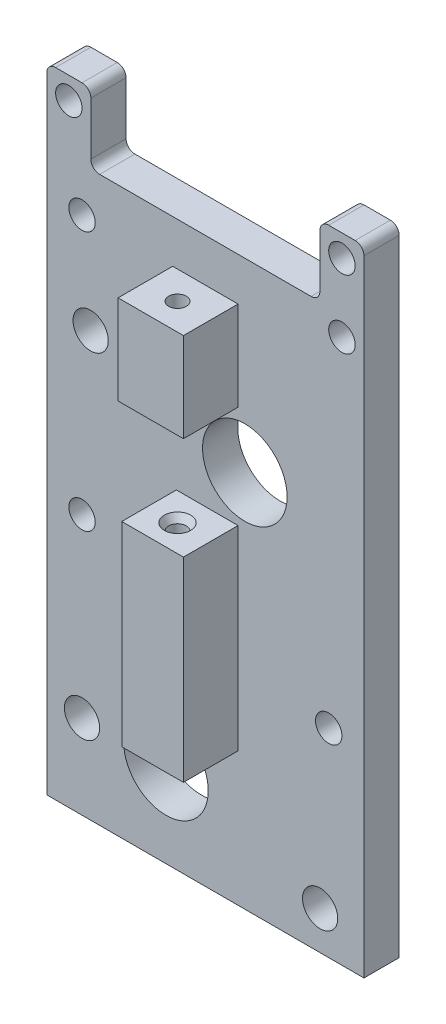
SolidWorks part; units mm, degrees
ref_plane "Front Plane" through (0, 0, 0) normal (0, 0, 1) x (1, 0, 0)
ref_plane "Top Plane" through (0, 0, 0) normal (0, 1, 0) x (1, 0, 0)
ref_plane "Right Plane" through (0, 0, 0) normal (1, 0, 0) x (0, 0, -1)
sketch "Sketch1" plane through (0, 0, 0) normal (0, 0, 1) x (1, 0, 0)
  line L0 (18, 32) -> (18, 39)
  line L1 (-18, -32) -> (18, -32)
  line L2 (-18, -32) -> (-18, 32)
  line L4 (18, -32) -> (18, 32)
  line L5 (-18, -32) -> (18, 32) construction
  line L6 (-18, 32) -> (18, -32) construction
  line L7 (-18, 32) -> (-18, 39)
  line L8 (-17, 40) -> (-14, 40)
  line L10 (-13, 39) -> (-13, 33)
  line L11 (-12, 32) -> (12, 32)
  line L12 (13, 33) -> (13, 39)
  line L13 (14, 40) -> (17, 40)
  arc A0 (18, 39) -> (17, 40) centre (17, 39) ccw
  arc A1 (13, 39) -> (14, 40) centre (14, 39) cw
  arc A2 (-13, 39) -> (-14, 40) centre (-14, 39) ccw
  arc A3 (-18, 39) -> (-17, 40) centre (-17, 39) cw
  arc A4 (12, 32) -> (13, 33) centre (12, 33) ccw
  arc A5 (-13, 33) -> (-12, 32) centre (-12, 33) ccw
  point P0 (0, 0)
  point P14 (13, 40)
  dimension "D1" = 1
  dimension "D2" = 1
extrude "Boss-Extrude1" add sketch "Sketch1" along normal blind 4
sketch "Sketch2" plane through (0, 0, 4) normal (0, 0, 1) x (1, 0, 0)
  line L2 (-4.475, -22.4429) -> (13.025, -22.4429) construction
  line L3 (4.475, 10.9277) -> (-13.025, 10.9277) construction
  line L4 (-13.025, 10.9277) -> (-13.025, 16.1277) construction
  line L5 (13.025, -22.4429) -> (13.025, -27.6429) construction
  circle A0 centre (15.5, 29.7441) radius 1.5
  circle A1 centre (-14, 27) radius 1.5
  circle A2 centre (4.475, 10.9277) radius 4.8
  circle A3 centre (-14, -2.4429) radius 1.5
  circle A4 centre (14, -9.4429) radius 1.5
  circle A5 centre (-4.475, -22.4429) radius 4.8
  circle A6 centre (13.025, -27.6429) radius 2
  circle A7 centre (-14, -22.4429) radius 2
  circle A8 centre (-13.025, 16.1277) radius 2
  circle A9 centre (15.5, 37.5) radius 1.5
  circle A10 centre (-15.5, 37.5) radius 1.5
extrude "Cut-Extrude1" cut sketch "Sketch2" against normal blind 10
sketch "Sketch3" plane through (0, 0, 4) normal (0, 0, 1) x (1, 0, 0)
  line L1 (-3.2906, -16.814) -> (3.7094, -16.814)
  line L2 (-3.2906, -16.814) -> (-3.2906, 5.3322)
  line L3 (-3.2906, 5.3322) -> (3.7094, 5.3322)
  line L4 (3.7094, -16.814) -> (3.7094, 5.3322)
  line L5 (-3.2906, -16.814) -> (3.7094, 5.3322) construction
  line L6 (-3.2906, 5.3322) -> (3.7094, -16.814) construction
  line L7 (-3.7094, 27.108) -> (3.7094, 27.108)
  line L8 (-3.7094, 27.108) -> (-3.7094, 16.9677)
  line L9 (-3.7094, 16.9677) -> (3.7094, 16.9677)
  line L10 (3.7094, 27.108) -> (3.7094, 16.9677)
  line L11 (-3.7094, 27.108) -> (3.7094, 16.9677) construction
  line L12 (-3.7094, 16.9677) -> (3.7094, 27.108) construction
  point P0 (0.2094, -5.7409)
  point P5 (0, 22.0378)
extrude "Boss-Extrude2" add sketch "Sketch3" along normal blind 6.2
sketch "Sketch4" plane through (0, -16.814, 0) normal (0, -1, 0) x (1, 0, 0)
  circle A0 centre (0, 7.165) radius 1
extrude "Cut-Extrude2" cut sketch "Sketch4" against normal blind 70
sketch "Sketch5" plane through (0, 5.3322, 0) normal (0, 1, 0) x (-1, 0, 0)
  circle A0 centre (0, 7.165) radius 1.5
extrude "Cut-Extrude3" cut sketch "Sketch5" against normal blind 3 draft 32
